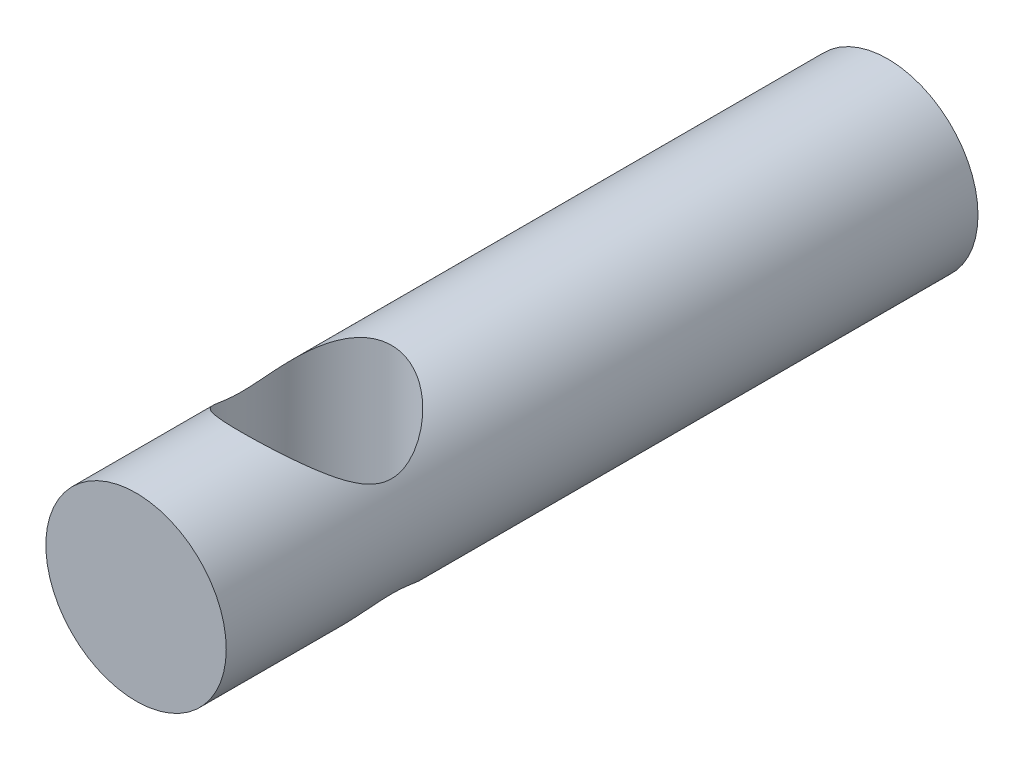
SolidWorks part; units mm, degrees
ref_plane "Front Plane" through (0, 0, 0) normal (0, 0, 1) x (1, 0, 0)
ref_plane "Top Plane" through (0, 0, 0) normal (0, 1, 0) x (1, 0, 0)
ref_plane "Right Plane" through (0, 0, 0) normal (1, 0, 0) x (0, 0, -1)
sketch "Sketch1" plane through (0, 0, 0) normal (0, 0, 1) x (1, 0, 0)
  circle A0 centre (0, 0) radius 6
  dimension "D1" = 12
extrude "Boss-Extrude1" add sketch "Sketch1" along normal blind 50
sketch "Sketch2" plane through (0, 0, 0) normal (0, 1, 0) x (1, 0, 0)
  circle A0 centre (0, -38) radius 5
  dimension "D2" = 10
  dimension "D1" = 38
extrude "Cut-Extrude1" cut sketch "Sketch2" against normal through all both and the other way through all
